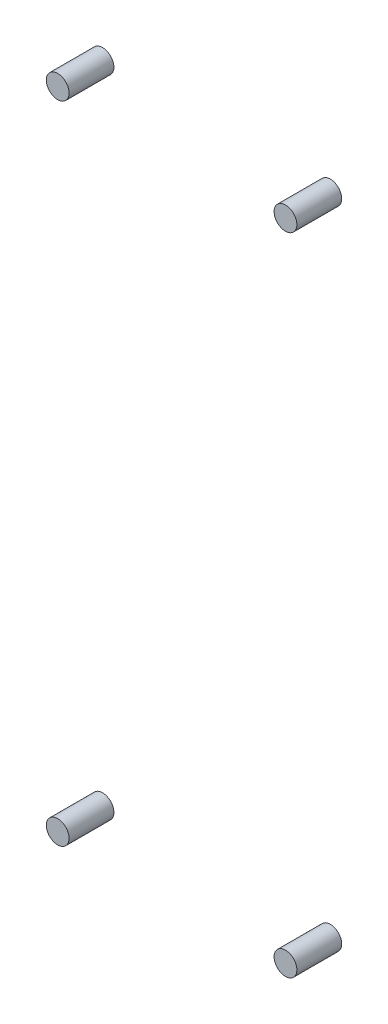
SolidWorks part; units mm, degrees
ref_plane "Front Plane" through (0, 0, 0) normal (0, 0, 1) x (1, 0, 0)
ref_plane "Top Plane" through (0, 0, 0) normal (0, 1, 0) x (1, 0, 0)
ref_plane "Right Plane" through (0, 0, 0) normal (1, 0, 0) x (0, 0, -1)
sketch "Sketch2" plane through (0, 0, 0) normal (0, 0, 1) x (1, 0, 0)
  line L0 (0, 0) -> (0, 6.6951) construction
  line L1 (0, 0) -> (-12.2936, 0) construction
  circle A0 centre (-7.62, 21.59) radius 0.762
  circle A1 centre (7.62, 21.59) radius 0.762
  circle A2 centre (7.62, -21.59) radius 0.762
  circle A3 centre (-7.62, -21.59) radius 0.762
  dimension "D1" = 1.524
  dimension "D2" = 1.524
  dimension "D3" = 15.24
  dimension "D4" = 7.62
  dimension "D5" = 21.59
extrude "Boss-Extrude2" add sketch "Sketch2" along normal blind 3
